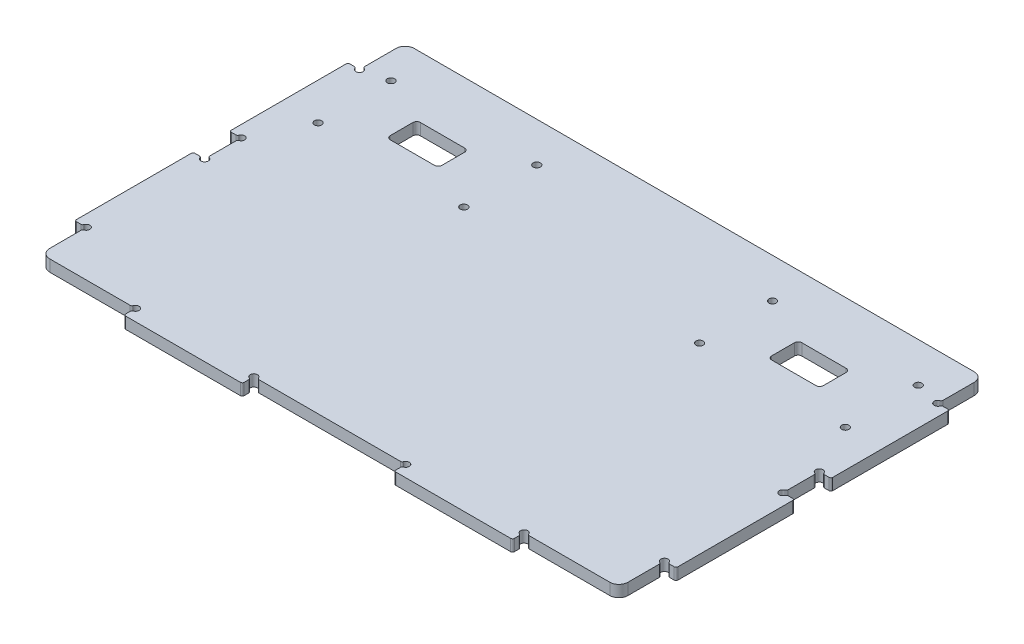
SolidWorks part; units mm, degrees
material "Maple"
ref_plane "Front Plane" through (0, 0, 0) normal (0, 0, 1) x (1, 0, 0)
ref_plane "Top Plane" through (0, 0, 0) normal (0, 1, 0) x (1, 0, 0)
ref_plane "Right Plane" through (0, 0, 0) normal (1, 0, 0) x (0, 0, -1)
sketch "Sketch1" plane through (0, 0, 0) normal (0, 1, 0) x (1, 0, 0)
  line L1 (-158.65, 181.66) -> (158.65, 181.66)
  line L2 (-158.65, 181.66) -> (-158.65, -181.66)
  line L3 (-158.65, -181.66) -> (158.65, -181.66)
  line L4 (158.65, 181.66) -> (158.65, -181.66)
  line L5 (-158.65, 181.66) -> (158.65, -181.66) construction
  line L6 (-158.65, -181.66) -> (158.65, 181.66) construction
  point P0 (0, 0)
  dimension "D1" = 317.3
  dimension "D2" = 363.32
extrude "Boss-Extrude1" add sketch "Sketch1" against normal blind 6.35
sketch "Sketch11" plane through (0, 0, 0) normal (0, 1, 0) x (1, 0, 0)
  line L0 (90.5067, -15.16) -> (118.8267, -15.16)
  line L1 (90.5067, -15.16) -> (90.5067, -31.66)
  line L2 (118.8267, -15.16) -> (118.8267, -31.66)
  line L3 (90.5067, -31.66) -> (118.8267, -31.66)
  line L4 (-158.65, -181.66) -> (158.65, -181.66) construction
  point P6 (104.6667, -31.66)
  dimension "D1" = 150
  dimension "D2" = 16.5
  dimension "D3" = 28.32
  dimension "D4" = 104.6667
extrude "Cut-Extrude8" cut sketch "Sketch11" against normal through all
sketch "Sketch12" plane through (0, 0, 0) normal (0, 1, 0) x (1, 0, 0)
  line L0 (118.8267, -31.66) -> (90.5067, -15.16) construction
  line L1 (64.6667, -3.41) -> (144.6667, -3.41) construction
  line L2 (64.6667, -3.41) -> (64.6667, -43.41) construction
  line L3 (144.6667, -3.41) -> (144.6667, -43.41) construction
  line L4 (64.6667, -43.41) -> (144.6667, -43.41) construction
  line L5 (64.6667, -43.41) -> (144.6667, -3.41) construction
  circle A0 centre (64.6667, -3.41) radius 2
  circle A1 centre (144.6667, -3.41) radius 2
  circle A2 centre (144.6667, -43.41) radius 2
  circle A3 centre (64.6667, -43.41) radius 2
  point P4 (104.6667, -23.41)
  point P7 (104.6667, -23.41)
  dimension "D3" = 4
  dimension "D1" = 40
  dimension "D2" = 80
extrude "Cut-Extrude9" cut sketch "Sketch12" against normal through all
mirror "Mirror3" about plane through (0, 0, 0) normal (1, 0, 0) of "Cut-Extrude9", "Cut-Extrude8"
fillet "Fillet4" radius 2 8 edges at (118.8267, -3.175, 15.16) (90.5067, -3.175, 15.16) (90.5067, -3.175, 31.66) (118.8267, -3.175, 31.66) (-90.5067, -3.175, 31.66) (-118.8267, -3.175, 31.66) (-90.5067, -3.175, 15.16) (-118.8267, -3.175, 15.16)
sketch "Sketch14" plane through (0, 0, 0) normal (0, 1, 0) x (1, 0, 0)
  line L0 (-158.65, 181.66) -> (-158.65, -181.66) construction
  line L1 (158.65, 181.66) -> (-158.65, 181.66)
  line L2 (158.65, 181.66) -> (158.65, 18.34)
  line L3 (158.65, 18.34) -> (-158.65, 18.34)
  line L4 (-158.65, 181.66) -> (-158.65, 18.34)
  line L5 (-158.65, -181.66) -> (158.65, -181.66) construction
  dimension "D1" = 200
extrude "Cut-Extrude10" cut sketch "Sketch14" against normal up to surface (6.35 mm away) up to face at (-64.6667, -6.35, 45.41)
sketch "Sketch15" plane through (0, 0, 0) normal (0, 1, 0) x (1, 0, 0)
  line L0 (158.65, -181.66) -> (158.65, 18.34) construction
  line L1 (158.65, -6.66) -> (165, -6.66)
  line L2 (158.65, -6.66) -> (158.65, -71.66)
  line L3 (158.65, -71.66) -> (165, -71.66)
  line L4 (165, -6.66) -> (165, -71.66)
  line L5 (-158.65, 18.34) -> (158.65, 18.34) construction
  dimension "D1" = 6.35
  dimension "D2" = 65
  dimension "D3" = 25
extrude "Boss-Extrude2" add sketch "Sketch15" against normal up to surface (6.35 mm away) up to face at (-64.6667, -6.35, 45.41)
sketch "Sketch16" plane through (0, 0, 0) normal (0, 1, 0) x (1, 0, 0)
  circle A0 centre (158.65, -71.66) radius 2
  circle A1 centre (158.65, -6.66) radius 2
  dimension "D1" = 4
extrude "Cut-Extrude11" cut sketch "Sketch16" against normal up to surface (6.35 mm away) up to face at (-64.6667, -6.35, 45.41)
fillet "Fillet5" radius 1 6 edges at (158.65, -3.175, 73.66) (160.65, -3.175, 71.66) (165, -3.175, 71.66) (165, -3.175, 6.66) (158.65, -3.175, 4.66) (160.65, -3.175, 6.66)
pattern_linear "LPattern1" count 2 spacing 85 along (0, 0, 1) of "Fillet5", "Cut-Extrude11", "Boss-Extrude2"
fillet "Fillet6" radius 5 4 edges at (-158.65, -3.175, 181.66) (-158.65, -3.175, -18.34) (158.65, -3.175, -18.34) (158.65, -3.175, 181.66)
sketch "Sketch18" plane through (0, 0, 0) normal (0, 1, 0) x (1, 0, 0)
  line L0 (-158.65, 13.34) -> (-158.65, -176.66) construction
  line L1 (-158.65, -6.66) -> (-165, -6.66)
  line L2 (-158.65, -6.66) -> (-158.65, -71.66)
  line L3 (-158.65, -71.66) -> (-165, -71.66)
  line L4 (-165, -6.66) -> (-165, -71.66)
  line L5 (-153.65, 18.34) -> (153.65, 18.34) construction
  dimension "D1" = 25
  dimension "D2" = 65
  dimension "D3" = 6.35
extrude "Boss-Extrude3" add sketch "Sketch18" against normal up to surface (6.35 mm away) up to face at (-64.6667, -6.35, 45.41)
sketch "Sketch19" plane through (0, 0, 0) normal (0, 1, 0) x (1, 0, 0)
  circle A0 centre (-158.65, -6.66) radius 2
  circle A1 centre (-158.65, -71.66) radius 2
  dimension "D1" = 4
extrude "Cut-Extrude12" cut sketch "Sketch19" against normal up to surface (6.35 mm away) up to face at (-64.6667, -6.35, 45.41)
fillet "Fillet7" radius 1 6 edges at (-158.65, -3.175, 73.66) (-160.65, -3.175, 71.66) (-165, -3.175, 71.66) (-165, -3.175, 6.66) (-160.65, -3.175, 6.66) (-158.65, -3.175, 4.66)
pattern_linear "LPattern2" count 2 spacing 85 along (0, 0, 1) of "Fillet7", "Cut-Extrude12", "Boss-Extrude3"
sketch "Sketch20" plane through (0, 0, 0) normal (0, 1, 0) x (1, 0, 0)
  line L0 (-153.65, -181.66) -> (153.65, -181.66) construction
  line L1 (41.65, -181.66) -> (106.65, -181.66)
  line L2 (41.65, -181.66) -> (41.65, -188.01)
  line L3 (41.65, -188.01) -> (106.65, -188.01)
  line L4 (106.65, -181.66) -> (106.65, -188.01)
  line L5 (158.65, -176.66) -> (158.65, -159.4884) construction
  dimension "D1" = 52
  dimension "D2" = 65
  dimension "D3" = 6.35
extrude "Boss-Extrude4" add sketch "Sketch20" against normal up to surface (6.35 mm away) up to face at (-64.6667, -6.35, 45.41)
sketch "Sketch21" plane through (0, 0, 0) normal (0, 1, 0) x (1, 0, 0)
  circle A0 centre (41.65, -181.66) radius 2
  circle A1 centre (106.65, -181.66) radius 2
  dimension "D1" = 4
extrude "Cut-Extrude13" cut sketch "Sketch21" against normal up to surface (6.35 mm away) up to face at (-64.6667, -6.35, 45.41)
fillet "Fillet8" radius 1 6 edges at (39.65, -3.175, 181.66) (41.65, -3.175, 183.66) (41.65, -3.175, 188.01) (106.65, -3.175, 188.01) (106.65, -3.175, 183.66) (108.65, -3.175, 181.66)
mirror "Mirror10" about plane through (0, 0, 0) normal (1, 0, 0) of "Cut-Extrude13", "Boss-Extrude4", "Fillet8"
